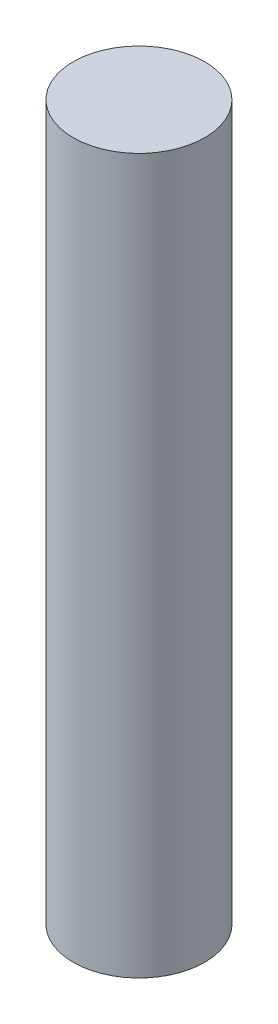
SolidWorks part; units mm, degrees
ref_plane "Front Plane" through (0, 0, 0) normal (0, 0, 1) x (1, 0, 0)
ref_plane "Top Plane" through (0, 0, 0) normal (0, 1, 0) x (1, 0, 0)
ref_plane "Right Plane" through (0, 0, 0) normal (1, 0, 0) x (0, 0, -1)
sketch "Sketch1" plane through (0, 0, 0) normal (0, 1, 0) x (1, 0, 0)
  circle A0 centre (0, 0) radius 44.45
  dimension "D1" = 88.9
extrude "Boss-Extrude1" add sketch "Sketch1" along normal blind 482.6
